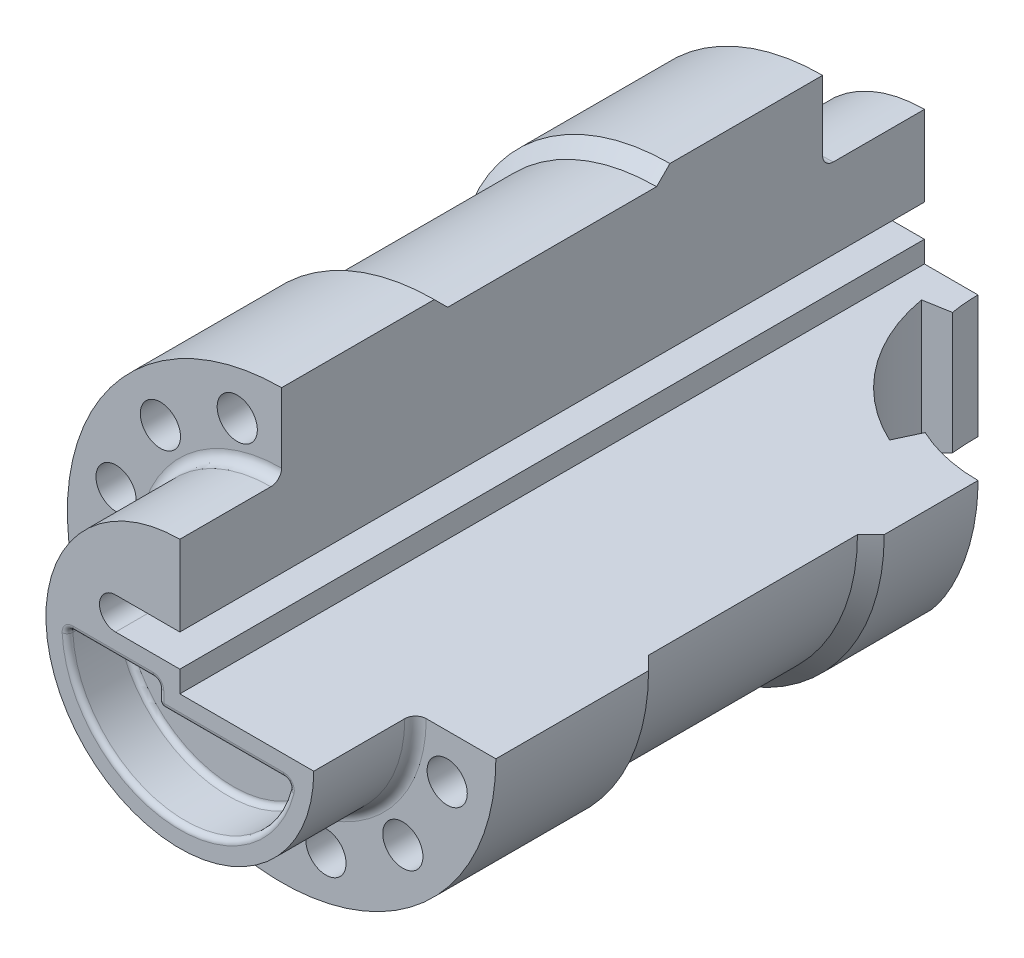
SolidWorks part; units mm, degrees
material "AISI 1020"
ref_plane "Front Plane" through (0, 0, 0) normal (0, 0, 1) x (1, 0, 0)
ref_plane "Top Plane" through (0, 0, 0) normal (0, 1, 0) x (1, 0, 0)
ref_plane "Right Plane" through (0, 0, 0) normal (1, 0, 0) x (0, 0, -1)
sketch "Sketch1" plane through (0, 0, 0) normal (0, 0, 1) x (1, 0, 0)
  line L0 (-12, 7) -> (0, 7) construction
  line L3 (0, 40) -> (0, 0)
  line L4 (0, 0) -> (40, 0)
  line L5 (-12, 10) -> (0, 10)
  line L6 (-12, 4) -> (0, 4)
  arc A0 (0, 40) -> (40, 0) centre (0, 0) ccw
  arc A2 (-12, 10) -> (-12, 4) centre (-12, 7) ccw
  point P4 (0, 7)
  dimension "D1" = 80
  dimension "D2" = 3
  dimension "D3" = 12
  dimension "D4" = 7
extrude "Boss-Extrude7" add sketch "Sketch1" along normal blind 139 contours A2 L5 L3 A0 L4 L6
sketch "Sketch8" plane through (0, 0, 139) normal (0, 0, 1) x (1, 0, 0)
  line L6 (0, 0) -> (40, 0)
  line L7 (0, 40) -> (0, 10)
  line L8 (25, 0) -> (40, 0)
  line L9 (0, 40) -> (0, 25)
  arc A0 (0, 25) -> (25, 0) centre (0, 0) ccw
  arc A4 (0, 40) -> (40, 0) centre (0, 0) ccw
  arc A5 (0, 40) -> (40, 0) centre (0, 0) ccw
  dimension "D1" = 50
  dimension "D2" = 0
extrude "Cut-Extrude1" cut sketch "Sketch8" against normal blind 19
sketch "Sketch9" plane through (0, 0, 0) normal (0, 0, -1) x (-1, 0, 0)
  line L6 (0, 0) -> (-40, 0)
  line L7 (0, 40) -> (0, 10)
  line L8 (-25, 0) -> (-40, 0)
  line L9 (0, 40) -> (0, 25)
  arc A0 (-25, 0) -> (0, 25) centre (0, 0) ccw
  arc A4 (-40, 0) -> (0, 40) centre (0, 0) ccw
  arc A5 (-40, 0) -> (0, 40) centre (0, 0) ccw
  dimension "D1" = 50
  dimension "D2" = 0
extrude "Cut-Extrude2" cut sketch "Sketch9" against normal blind 19
fillet "Fillet5" radius 2 1 edges at (-17.6777, -17.6777, 120)
fillet "Fillet6" radius 2 1 edges at (-17.6777, -17.6777, 19)
sketch "Sketch10" plane through (0, 0, 0) normal (1, 0, 0) x (0, 0, -1)
  line L0 (-47.5, 40) -> (-50, 37.5)
  line L1 (-120, 40) -> (-19, 40) construction
  line L2 (-50, 37.5) -> (-89, 37.5)
  line L3 (-89, 37.5) -> (-91.5, 40)
  line L4 (-91.5, 40) -> (-47.5, 40)
  dimension "D1" = 2.5
  dimension "D2" = 45
  dimension "D3" = 45
  dimension "D4" = 28.5
  dimension "D5" = 28.5
revolve "Cut-Revolve6" cut sketch "Sketch10" about axis through (0, 0, 139) along (0, 0, -1)
sketch "Sketch11" plane through (0, 0, 120) normal (0, 0, 1) x (1, 0, 0)
  line L0 (0, 0) -> (-10.3528, 38.637) construction
  line L1 (0, 27) -> (0, 40) construction
  arc A0 (-4.6093, 31.6663) -> (19.825, 25.1191) centre (0, 0) ccw construction
  arc A1 (0, 40) -> (40, 0) centre (0, 0) ccw construction
  circle A2 centre (-8.2822, 30.9096) radius 3.75
  arc A4 (-4.6093, 31.6663) -> (19.825, 25.1191) centre (0, 0) ccw construction
  circle A6 centre (0, 0) radius 32 construction
  circle A8 centre (0, 0) radius 32 construction
  circle A9 centre (30.9096, -8.2822) radius 3.75
  circle A10 centre (0, 0) radius 32 construction
  circle A11 centre (22.6274, -22.6274) radius 3.75
  circle A12 centre (0, 0) radius 32 construction
  circle A13 centre (8.2822, -30.9096) radius 3.75
  circle A14 centre (0, 0) radius 32 construction
  circle A15 centre (-8.2822, -30.9096) radius 3.75
  circle A16 centre (0, 0) radius 32 construction
  circle A17 centre (-22.6274, -22.6274) radius 3.75
  circle A18 centre (0, 0) radius 32 construction
  circle A19 centre (-30.9096, -8.2822) radius 3.75
  circle A20 centre (0, 0) radius 32 construction
  circle A21 centre (-30.9096, 8.2822) radius 3.75
  circle A22 centre (0, 0) radius 32 construction
  circle A23 centre (-22.6274, 22.6274) radius 3.75
  circle A24 centre (0, 0) radius 32 construction
  arc A25 (4.6093, 31.6663) -> (11.8413, 29.7285) centre (8.2822, 30.9096) ccw [skipped]
  arc A26 (19.825, 25.1191) -> (25.1191, 19.825) centre (22.6274, 22.6274) ccw [skipped]
  arc A27 (31.6663, 4.6093) -> (29.7285, 11.8413) centre (30.9096, 8.2822) ccw [skipped]
  point P47 (0, 0)
  dimension "D1" = 64
  dimension "D3" = 7.5
  dimension "D2" = 15
  dimension "D4" = 12
extrude "Cut-Extrude3" cut sketch "Sketch11" against normal through all
sketch "Sketch12" plane through (0, 0, 0) normal (0, 1, 0) x (1, 0, 0)
  line L0 (25, 0) -> (40, 0)
  line L1 (40, 0) -> (40, -19)
  line L3 (10, 0) -> (25, 0)
  line L4 (40, -19) -> (40, -30)
  line L5 (40, 0) -> (5.5317, -6.0777) construction
  line L6 (40, 0) -> (25.2084, -31.7208) construction
  line L7 (0, 0) -> (25, 0) construction
  line L8 (5.5317, -6.0777) -> (10.4558, -5.2094)
  line L9 (25.2084, -31.7208) -> (27.3215, -27.1892)
  arc A0 (10, 0) -> (40, -30) centre (40, 0) ccw
  arc A1 (5.5317, -6.0777) -> (25.2084, -31.7208) centre (40, 0) ccw
  line M4 (40, -47.5) -> (40, -19)
  line M5 (40, -19) -> (27, -19)
  arc M6 (27, -19) -> (25, -17) centre (27, -17) cw
  line M7 (25, -17) -> (25, 0)
  line M8 (25, 0) -> (0, 0)
  dimension "D1" = 70
  dimension "D2" = 60
  dimension "D3" = 10
  dimension "D4" = 25
extrude "Cut-Extrude4" cut sketch "Sketch12" against normal through all contours A0 M8 M4 M5 M6 M7 | L8 A1 L9 A0
sketch "Sketch16" plane through (0, 0, 139) normal (0, 0, 1) x (1, 0, 0)
  line L15 (20.6155, -4) -> (-4, -4)
  line L16 (-4, -4) -> (-4, 0)
  line L17 (-4, 0) -> (-21, 0)
  arc A6 (-21, 0) -> (20.6155, -4) centre (0, 0) ccw
  point P0 (-21, 0)
  dimension "D1" = 4
extrude "Cut-Extrude5" cut sketch "Sketch16" against normal blind 10
fillet "Fillet7" radius 1 12 edges at (-4, -2, 129) (-4, -2, 139) (-2.0092, -20.9037, 129) (-2.0092, -20.9037, 139) (20.6155, -4, 134) (8.3078, -4, 129) (-4, -4, 134) (8.3078, -4, 139) (-4, 0, 134) (-12.5, 0, 129) (-21, 0, 134) (-12.5, 0, 139)
